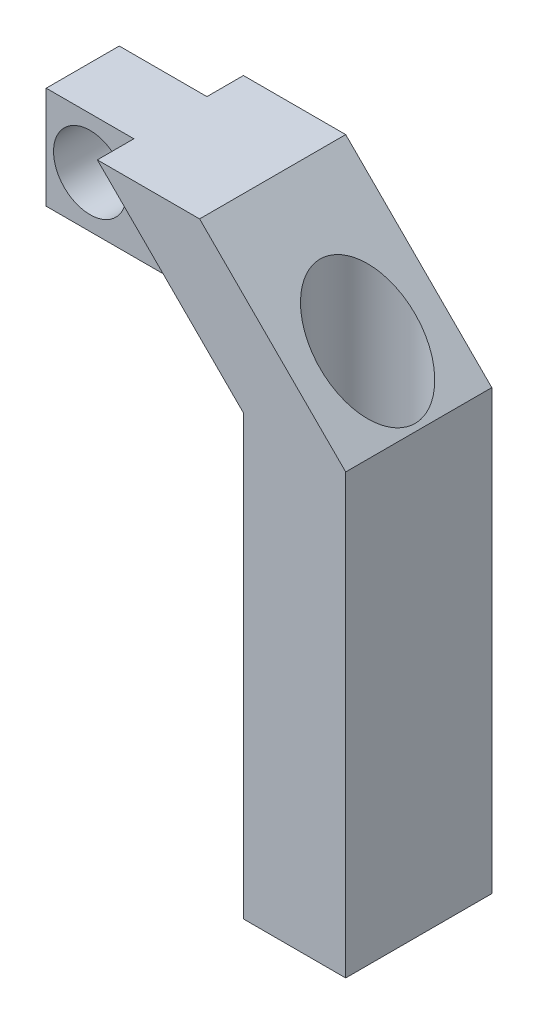
SolidWorks part; units mm, degrees
ref_plane "Front Plane" through (0, 0, 0) normal (0, 0, 1) x (1, 0, 0)
ref_plane "Top Plane" through (0, 0, 0) normal (0, 1, 0) x (1, 0, 0)
ref_plane "Right Plane" through (0, 0, 0) normal (1, 0, 0) x (0, 0, -1)
sketch "Sketch2" plane through (0, 0, 0) normal (0, 0, 1) x (1, 0, 0)
  line L0 (0, 0) -> (-7, 0)
  line L1 (0, 0) -> (-10, 10)
  line L2 (-7, 0) -> (-17, 10)
  line L3 (-10, 10) -> (-17, 10)
  dimension "D1" = 7
  dimension "D2" = 10
  dimension "D3" = 10
extrude "Boss-Extrude2" add sketch "Sketch2" along normal mid plane 10
sketch "Sketch3" plane through (0, 0, 0) normal (0, -1, 0) x (1, 0, 0)
  line L0 (-7, 0) -> (0, 0) construction
  line L1 (-7, 5) -> (-7, -5) construction
  circle A0 centre (-3.5, 0) radius 3.25
  dimension "D1" = 6.5
extrude "Cut-Extrude1" cut sketch "Sketch3" against normal through all
sketch "Sketch4" plane through (0, 0, 0) normal (0, 0, 1) x (1, 0, 0)
  line L0 (-17, 10) -> (-7, 0) construction
  line L1 (-10, 3) -> (-23, 3)
  line L2 (-10, 3) -> (-10, 10)
  line L3 (-10, 10) -> (-23, 10)
  line L4 (-23, 3) -> (-23, 10)
  line L5 (-16.5, 10) -> (-16.5, 3) construction
  line L6 (-10, 6.5) -> (-23, 6.5) construction
  line L7 (-10, 10) -> (-17, 10) construction
  point P328 (-16.5, 6.5)
  dimension "D1" = 7
  dimension "D2" = 6
extrude "Boss-Extrude3" add sketch "Sketch4" along normal mid plane 5
sketch "Sketch5" plane through (0, 0, 2.5) normal (0, 0, 1) x (1, 0, 0)
  line L0 (-23, 10) -> (-23, 3) construction
  line L1 (-23, 6.5) -> (-13.5, 6.5) construction
  line L2 (-17, 10) -> (-10, 3) construction
  circle A0 centre (-20, 6.5) radius 2.5
  dimension "D1" = 5
  dimension "D2" = 3
extrude "Cut-Extrude2" cut sketch "Sketch5" against normal through all
sketch "Sketch6" plane through (0, 0, 0) normal (0, -1, 0) x (1, 0, 0)
  line L1 (0, 5) -> (-7, 5)
  line L2 (0, 5) -> (0, -5)
  line L3 (0, -5) -> (-7, -5)
  line L4 (-7, 5) -> (-7, -5)
  line L5 (-3.5, -5) -> (-3.5, 5) construction
  line L6 (0, 0) -> (-7, 0) construction
  circle A0 centre (-3.5, 0) radius 3.25
  point P72 (-3.5, 0)
extrude "Boss-Extrude4" add sketch "Sketch6" along normal blind 30
